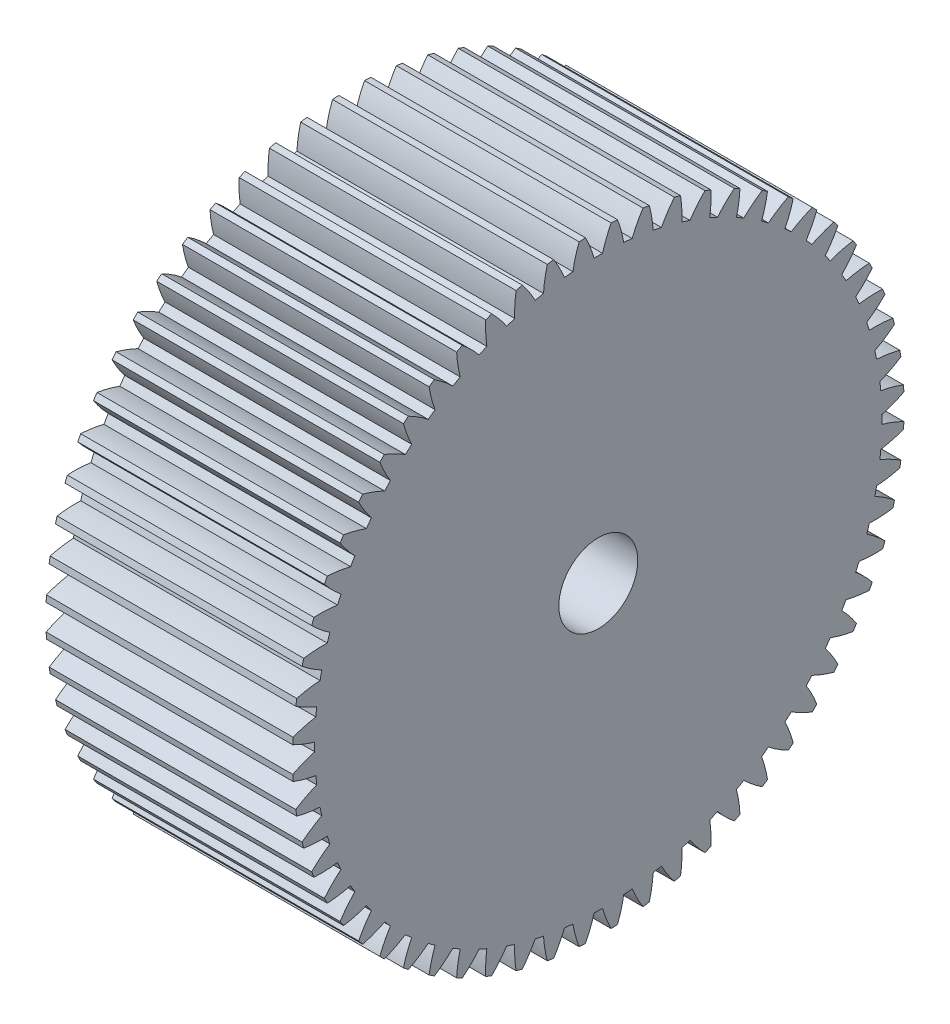
SolidWorks part; units mm, degrees
ref_plane "Plane1" through (0, 0, 0) normal (0, 0, 1) x (1, 0, 0)
ref_plane "Plane2" through (0, 0, 0) normal (0, 1, 0) x (1, 0, 0)
ref_plane "Plane3" through (0, 0, 0) normal (1, 0, 0) x (0, 0, -1)
other "Configuration Table"
sketch "HoldingSke" plane through (0, 0, 0) normal (0, 1, 0) x (1, 0, 0)
  line L0 (0, 0) -> (0.5, -0.866)
  line L1 (-15, 0) -> (100, 0) construction
  line L2 (0, 0) -> (-2.1039, 2.3779)
  line L3 (0, 0) -> (-11.863, 4.5341)
  line L4 (0, 0) -> (4.318, 7.479)
  line L5 (0, 0) -> (-46.8476, -17.4728)
  line L6 (0, 0) -> (-20.7241, -13.9826)
  line L7 (-2.1039, 2.3779) -> (8.6586, 51.2059)
  line L8 (-76.2, 54.61) -> (-74.8, 54.61)
  line L9 (-71.009, 38.7566) -> (-53.1078, 45.2721)
  line L10 (-76.2, 71.12) -> (104.1128, 71.12)
  line L11 (0, 0) -> (-25, 0)
  line L12 (-76.2, 101.6) -> (-76.162, 101.6)
  line L13 (24.9733, 27.94) -> (52.9518, 28.4284)
  line L14 (24.9733, 27.94) -> (24.9743, 27.94)
  line L15 (24.9733, 27.94) -> (100.4006, 29.5858)
  line L16 (-63.627, -1) -> (-12.827, -1)
  circle A0 centre (0, 0) radius 4
  circle A1 centre (0, 0) radius 28.749
  circle A2 centre (0, 0) radius 37.5
  circle A3 centre (0, 0) radius 4
  dimension "MHD" = 57.498
  dimension "Hub_dia" = 75
  dimension "Bore" = 8
  dimension "MBD" = 8
  dimension "Num_teeth" = 60
  dimension "Pitch" = 1
  dimension "Overall_len" = 50
  dimension "Show_teeth" = 60
  dimension "Thickness" = 25
  dimension "OAL" = 50.0001
  dimension "T_dim" = 1.4
  dimension "Ap" = 20
  dimension "H" = 19.05
  dimension "Pitch_radius" = 180.3128
  dimension "Width" = 25
  dimension "Backlash" = 0.038
  dimension "Addendum_fac" = 1
  dimension "Dedendum_fac" = 1.25
  dimension "Clearance_fac" = 0.25
  dimension "Dedendum_add" = 0.001
  dimension "Module" = 1
sketch "BasProSke" plane through (0, 0, 0) normal (0, 1, 0) x (1, 0, 0)
  line L0 (-10, 0) -> (60, 0) construction
  line L1 (0, 0) -> (0, 31)
  line L2 (0, 0) -> (25, 0)
  line L3 (25, 0) -> (25, 31)
  line L4 (25, 31) -> (0, 31)
  dimension "Thickness" = 25
  dimension "Diameter" = 62
revolve "Base-Revolve" add sketch "BasProSke" angle 360 about L0
sketch "TooCutSke" plane through (0, 0, 0) normal (1, 0, 0) x (0, 0, -1)
  line L1 (0, 0) -> (0, 107) construction
  line L2 (0, 0) -> (-0.8518, 29.9879) construction
  line L3 (0, 0) -> (-3.1393, 59.9006) construction
  line L4 (-0.8518, 29.9879) -> (-1.5696, 29.9503) construction
  arc A0 (0.4302, 28.7458) -> (-0.4302, 28.7458) centre (0, 0) ccw
  arc A1 (1.3127, 30.9976) -> (-1.3127, 30.9976) centre (0, 0) ccw
  circle A2 centre (0, 0) radius 30 construction
  circle A3 centre (0, 0) radius 28.1908 construction
  arc A4 (-0.4302, 28.7458) -> (-1.3127, 30.9976) centre (-11.9871, 25.5153) ccw
  arc A5 (1.3127, 30.9976) -> (0.4302, 28.7458) centre (11.9871, 25.5153) ccw
  dimension "Root_dia" = 57.498
  dimension "Overcut_dia" = 62.0508
  dimension "Pitch_dia" = 60
  dimension "Base_dia" = 56.3816
  dimension "Flank_rad" = 12
  dimension "Half_ang" = 3
  dimension "Half_CT" = 0.7188
extrude "ToothCut" cut sketch "TooCutSke" along normal through all
fillet "Breaks" [suppressed] radius 0.02
fillet "RootFillets" [suppressed] radius 0.251
pattern_circular "TeethCuts" count 60 every 6 about axis through (-10, 0, 0) along (1, 0, 0) of "ToothCut", "RootFillets", "Breaks"
sketch "HubNeaOneSke" plane through (0, 0, 0) normal (-1, 0, 0) x (0, 0, 1)
  circle A0 centre (0, 0) radius 28.749
  dimension "Diameter" = 57.498
extrude "HubNearOne" [suppressed] add sketch "HubNeaOneSke" along normal blind 25.0001
sketch "HubNeaBotSke" plane through (0, 0, 0) normal (-1, 0, 0) x (0, 0, 1)
  circle A0 centre (0, 0) radius 28.749
  dimension "Diameter" = 57.498
extrude "HubNearBoth" [suppressed] add sketch "HubNeaBotSke" along normal blind 12.5
ref_plane "FarPln" through (25, 0, 0) normal (1, 0, 0) x (0, 0, -1)
sketch "HubFarSke" plane through (25, 0, 0) normal (1, 0, 0) x (0, 0, -1)
  circle A0 centre (0, 0) radius 28.749
  dimension "Diameter" = 57.498
extrude "HubFar" [suppressed] add sketch "HubFarSke" along normal blind 12.5
sketch "BorSke" plane through (0, 0, 0) normal (1, 0, 0) x (0, 0, -1)
  circle A0 centre (0, 0) radius 4
  dimension "Diameter" = 8
extrude "Bore" cut sketch "BorSke" along normal mid plane 100.0001
sketch "KeySke" plane through (0, 0, 0) normal (1, 0, 0) x (0, 0, -1)
  line L0 (-1.5, 0) -> (-1.5, 5.4)
  line L1 (-1.5, 5.4) -> (1.5, 5.4)
  line L2 (1.5, 5.4) -> (1.5, 0)
  line L3 (0, 0) -> (0, 34) construction
  line L4 (-1.5, 0) -> (1.5, 0)
  dimension "Offset" = 5.4
  dimension "Width" = 3
extrude "Keyway" [suppressed] cut sketch "KeySke" along normal mid plane 100.0001
pattern_circular "Keyway2" [suppressed] count 2 every 90 about axis through (-10, 0, 0) along (1, 0, 0)
equation "' \"Module@HoldingSke\" = 6.35"
equation "' \"Num_teeth@HoldingSke\" = 12"
equation "' \"Ap@HoldingSke\" =  20"
equation "' \"Ap@HoldingSke\" = 20"
equation "' \"Width@HoldingSke\" = 0.5 * 25.4"
equation "' \"Hub_dia@HoldingSke\"= 1 * 25.4"
equation "' \"Hub_dia@HoldingSke\" = 1 * 25.4"
equation "' \"Overall_len@HoldingSke\" = 1.0 * 25.4"
equation "' \"Bore@HoldingSke\" = 0.75 * 25.4"
equation "' \"T_dim@HoldingSke\" = 0.1 * 25.4"
equation "' \"Width@KeySke\" = 0.25 * 25.4"
equation "' \"Show_teeth@HoldingSke\" = 13"
equation "' \"Backlash@HoldingSke\" = 0.009 * 25.4"
equation "' \"Addendum_fac@HoldingSke\" = 1.0"
equation "' \"Dedendum_fac@HoldingSke\" = 1.25"
equation "' \"Dedendum_add@HoldingSke\" = 0.00005 * 25.4"
equation "' \"Clearance_fac@HoldingSke\" = 0.25"
equation "\"Pitch@HoldingSke\" = 1 / \"Module@HoldingSke\""
equation "\"Overcut_dia@TooCutSke\" = (\"Num_teeth@HoldingSke\" + 2 * \"Addendum_fac@HoldingSke\") / \"Pitch@HoldingSke\" + 0.002 * 25.4"
equation "\"Pitch_dia@TooCutSke\" = \"Num_teeth@HoldingSke\" / \"Pitch@HoldingSke\""
equation "\"Base_dia@TooCutSke\" = \"Num_teeth@HoldingSke\" / \"Pitch@HoldingSke\" * cos((\"Ap@HoldingSke\"  * 3.14159265 / 180))"
equation "\"Root_dia@TooCutSke\" = (\"Num_teeth@HoldingSke\" + 2) / \"Pitch@HoldingSke\" - 2 * (\"Addendum_fac@HoldingSke\" + \"Dedendum_fac@HoldingSke\") / \"Pitch@HoldingSke\" - \"Dedendum_add@HoldingSke\" * 2"
equation "\"Half_ang@TooCutSke\" = 180 / \"Num_teeth@HoldingSke\""
equation "\"Half_CT@TooCutSke\" = \"Num_teeth@HoldingSke\" / \"Pitch@HoldingSke\" * sin((3.14159265 / 2 / \"Num_teeth@HoldingSke\")) / 2 - 7 * \"Backlash@HoldingSke\" / 4"
equation "\"Flank_rad@TooCutSke\" = \"Num_teeth@HoldingSke\" / \"Pitch@HoldingSke\" / 5"
equation "\"Radius@RootFillets\" = \"Clearance_fac@HoldingSke\" / \"Pitch@HoldingSke\" + \"Dedendum_add@HoldingSke\""
equation "\"Break_rad@Breaks\" = 0.02 / \"Pitch@HoldingSke\""
equation "\"Thickness@HoldingSke\" = \"Width@HoldingSke\""
equation "\"OAL@HoldingSke\" = \"Thickness@HoldingSke\""
equation "\"MHD@HoldingSke\" = (\"Num_teeth@HoldingSke\" + 2) / \"Pitch@HoldingSke\" - 2 * (\"Addendum_fac@HoldingSke\" + \"Dedendum_fac@HoldingSke\")  / \"Pitch@HoldingSke\" - \"Dedendum_add@HoldingSke\" * 2"
equation "\"MBD@HoldingSke\" = (\"Num_teeth@HoldingSke\" + 2) / \"Pitch@HoldingSke\" - 2 * (\"Addendum_fac@HoldingSke\" + \"Dedendum_fac@HoldingSke\")  / \"Pitch@HoldingSke\" - \"Dedendum_add@HoldingSke\" * 2 - 0.002 * 25.4"
equation "\"MHD@HoldingSke\" = ((sgn( \"MHD@HoldingSke\" - \"Hub_dia@HoldingSke\" )-1)*( \"MHD@HoldingSke\" - \"Hub_dia@HoldingSke\" ))/-2+ \"Hub_dia@HoldingSke\""
equation "\"MBD@HoldingSke\" = ((sgn( \"MBD@HoldingSke\" - \"Bore@HoldingSke\" )-1)*( \"MBD@HoldingSke\" - \"Bore@HoldingSke\" ))/-2+ \"Bore@HoldingSke\""
equation "\"OAL@HoldingSke\" = ((sgn( \"OAL@HoldingSke\" - \"Overall_len@HoldingSke\" )+1)*( \"OAL@HoldingSke\" - \"Overall_len@HoldingSke\" ))/2 + \"Overall_len@HoldingSke\" + 0.000002 * 25.4"
equation "\"Num_teeth@TeethCuts\" = int( \"Show_teeth@HoldingSke\" ) + 1"
equation "\"Num_teeth@TeethCuts\" = ((sgn( \"Num_teeth@TeethCuts\" - \"Num_teeth@HoldingSke\" )-1)*( \"Num_teeth@TeethCuts\" - \"Num_teeth@HoldingSke\" ))/-2+ \"Num_teeth@HoldingSke\""
equation "\"Num_teeth@TeethCuts\" = ((sgn( \"Num_teeth@TeethCuts\" - 2.0)+1)*( \"Num_teeth@TeethCuts\" - 2.0))/2 +2.0"
equation "\"Angle@TeethCuts\" = 360.0 / \"Num_teeth@HoldingSke\""
equation "\"Diameter@BasProSke\" = (\"Num_teeth@HoldingSke\" + 2 * \"Addendum_fac@HoldingSke\") / \"Pitch@HoldingSke\""
equation "\"Thickness@BasProSke\"  = \"Thickness@HoldingSke\""
equation "' \"Fillet_rad@BasProSke\" =  \"Thickness@HoldingSke\" * 0.05"
equation "' \"Fillet_rad@BasProSke\" = \"Thickness@HoldingSke\" * 0.05"
equation "\"MHD@HoldingSke\" = ((sgn( \"MHD@HoldingSke\" - \"Root_dia@TooCutSke\" )-1)*( \"MHD@HoldingSke\" - \"Root_dia@TooCutSke\" ))/-2+ \"Root_dia@TooCutSke\""
equation "\"Diameter@HubNeaOneSke\" = \"MHD@HoldingSke\""
equation "\"Length@HubNearOne\" = \"OAL@HoldingSke\" - \"Thickness@BasProSke\""
equation "\"Diameter@HubNeaBotSke\" = \"MHD@HoldingSke\""
equation "\"Length@HubNearBoth\" = ( \"OAL@HoldingSke\" - \"Thickness@BasProSke\" ) / 2.0"
equation "\"Thickness@FarPln\" = \"Thickness@BasProSke\""
equation "\"Diameter@HubFarSke\" = \"MHD@HoldingSke\""
equation "\"Length@HubFar\" = ( \"OAL@HoldingSke\" - \"Thickness@BasProSke\" ) / 2.0"
equation "\"Diameter@BorSke\" = \"MBD@HoldingSke\""
equation "\"D1@Bore\" = \"OAL@HoldingSke\" * 2.0"
equation "\"D1@Keyway\" = \"OAL@HoldingSke\" * 2.0"
equation "\"Offset@KeySke\" = \"T_dim@HoldingSke\" + \"MBD@HoldingSke\" / 2.0"
